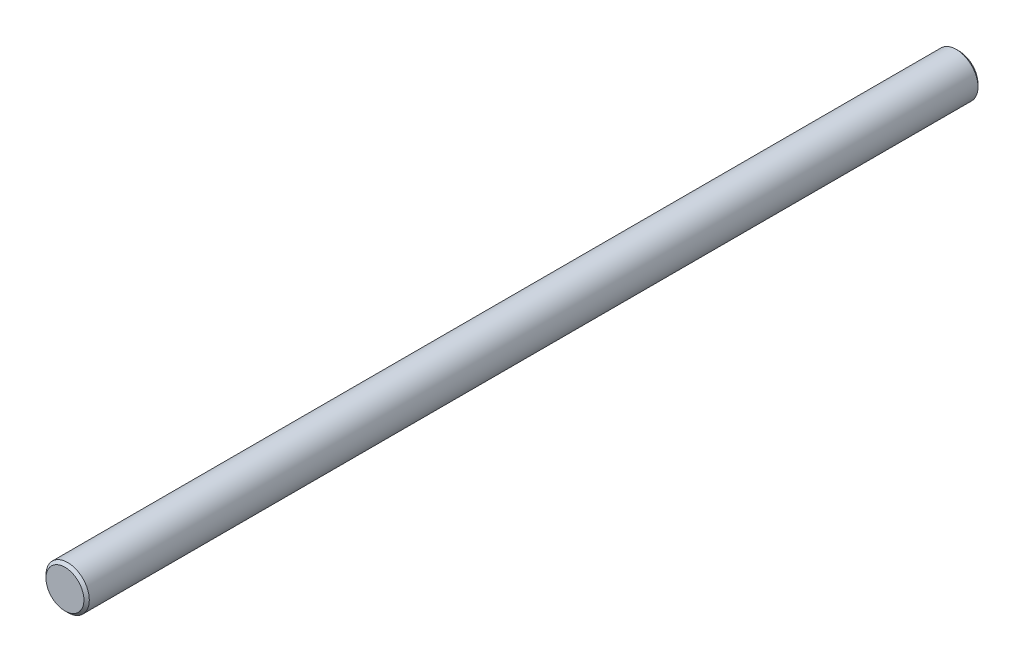
SolidWorks part; units mm, degrees
material "AISI 1020 Steel, Cold Rolled"
ref_plane "Front Plane" through (0, 0, 0) normal (0, 0, 1) x (1, 0, 0)
ref_plane "Top Plane" through (0, 0, 0) normal (0, 1, 0) x (1, 0, 0)
ref_plane "Right Plane" through (0, 0, 0) normal (1, 0, 0) x (0, 0, -1)
sketch "Sketch1" plane through (0, 0, 0) normal (0, 0, 1) x (1, 0, 0)
  circle A0 centre (0, 0) radius 4
  dimension "D1" = 8
extrude "Boss-Extrude1" add sketch "Sketch1" along normal blind 165
chamfer "Chamfer1" distance 0.5 angle 45 2 edges at (4, 0, 0) (4, 0, 165)
